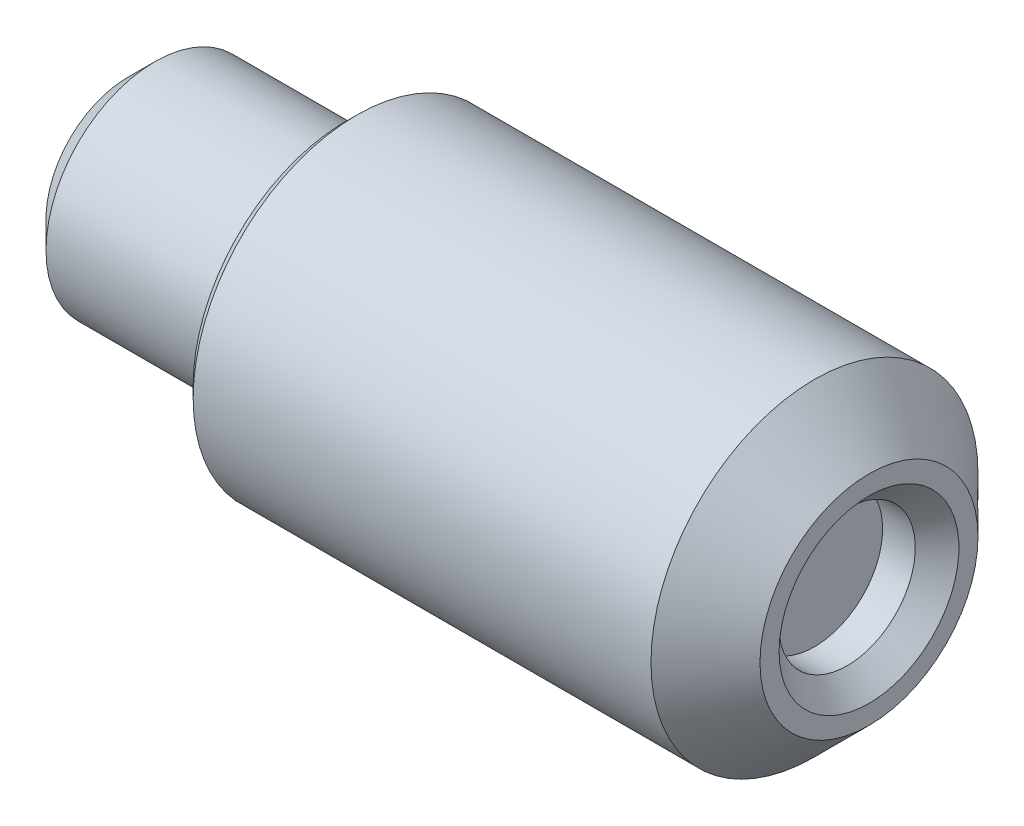
SolidWorks part; units mm, degrees
ref_plane "Plan de face" through (0, 0, 0) normal (0, 0, 1) x (1, 0, 0)
ref_plane "Plan de dessus" through (0, 0, 0) normal (0, 1, 0) x (1, 0, 0)
ref_plane "Plan de droite" through (0, 0, 0) normal (1, 0, 0) x (0, 0, -1)
sketch "Esquisse1" plane through (0, 0, 0) normal (0, 0, 1) x (1, 0, 0)
  line L0 (0, 0) -> (22.9545, 0) construction
  line L1 (0, 0) -> (0, 1.25) construction
  line L2 (-1, 0) -> (-1, 1.25)
  line L3 (-1, 1.25) -> (0, 1.25)
  line L4 (0, 3) -> (-9.6, 3)
  line L5 (-9.6, 3) -> (-9.6, 2)
  line L6 (-9.6, 2) -> (-13.6, 2)
  line L7 (-13.6, 2) -> (-13.6, 0)
  line L8 (-13.6, 0) -> (-1, 0)
  line L9 (0, 3) -> (0, 1.25)
  line L10 (-1, 0) -> (0, 0) construction
  dimension "D1" = 1
  dimension "D2" = 4
  dimension "D3" = 6
  dimension "D4" = 2.5
  dimension "D5" = 13.6
  dimension "D6" = 4
revolve "Révolution1" add sketch "Esquisse1" angle 360 about L0
chamfer "Chanfrein2" distance 1 angle 45 1 edges at (0, 0, 3)
chamfer "Chanfrein3" distance 0.4 angle 45 1 edges at (0, 0, 1.25)
chamfer "Chanfrein4" distance 0.2 angle 45 1 edges at (-9.6, 0, 3)
chamfer "Chanfrein5" distance 0.5 angle 45 1 edges at (-13.6, 0, 2)
